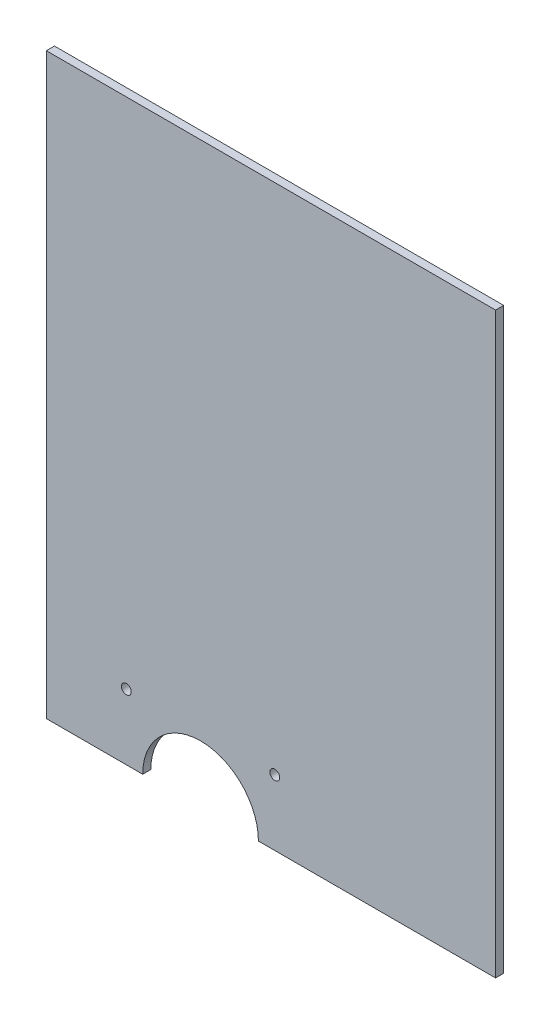
SolidWorks part; units mm, degrees
ref_plane "Plan de face" through (0, 0, 0) normal (0, 0, 1) x (1, 0, 0)
ref_plane "Plan de dessus" through (0, 0, 0) normal (0, 1, 0) x (1, 0, 0)
ref_plane "Plan de droite" through (0, 0, 0) normal (1, 0, 0) x (0, 0, -1)
sketch "Esquisse1" plane through (0, 0, 0) normal (0, 0, 1) x (1, 0, 0)
  line L1 (-119.563, 68.7323) -> (113.437, 68.7323)
  line L2 (-119.563, 68.7323) -> (-119.563, -231.2677)
  line L3 (-119.563, -231.2677) -> (113.437, -231.2677)
  line L4 (113.437, 68.7323) -> (113.437, -231.2677)
  dimension "D1" = 233
  dimension "D2" = 300
extrude "Boss.-Extru.1" add sketch "Esquisse1" along normal blind 4.2
sketch "Esquisse2" plane through (0, 0, 4.2) normal (0, 0, 1) x (1, 0, 0)
  line L0 (-69.563, -231.2677) -> (-9.563, -231.2677)
  line L2 (-119.563, -231.2677) -> (113.437, -231.2677) construction
  arc A1 (-69.563, -231.2677) -> (-9.563, -231.2677) centre (-39.563, -231.2677) cw
  circle A2 centre (-78.063, -197.2677) radius 2.55
  circle A3 centre (-1.063, -197.2677) radius 2.55
  point P7 (-14.2646, -220.3954)
  point P8 (-9.5843, -230.141)
  point P9 (-10.2544, -232.8719)
  point P10 (-9.9623, -231.2677)
  point P14 (-69.563, -231.2677)
  dimension "D2" = 30
  dimension "D4" = 5.1
  dimension "D5" = 5.1
  dimension "D1" = 50
  dimension "D3" = 0
  dimension "D6" = 34
  dimension "D7" = 0
  dimension "D8" = 77
  dimension "D9" = 38.5
extrude "Enlèv. mat.-Extru.1" cut sketch "Esquisse2" against normal through all
